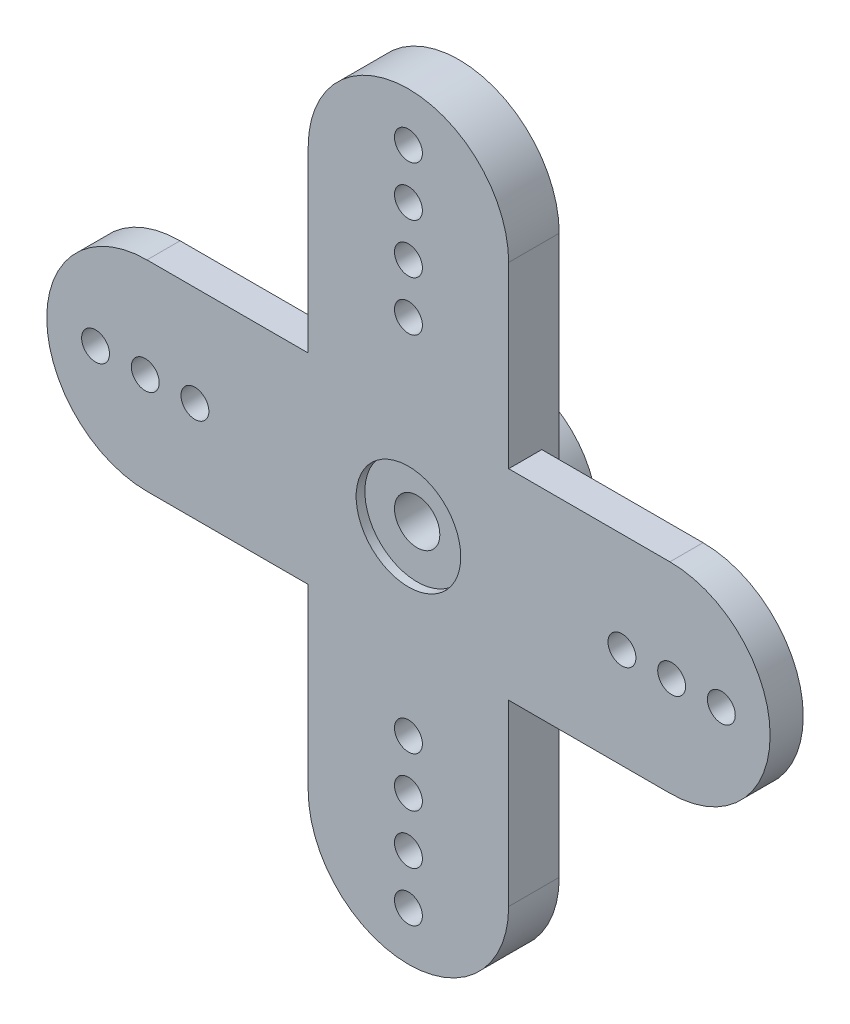
SolidWorks part; units mm, degrees
ref_plane "Front Plane" through (0, 0, 0) normal (0, 0, 1) x (1, 0, 0)
ref_plane "Top Plane" through (0, 0, 0) normal (0, 1, 0) x (1, 0, 0)
ref_plane "Right Plane" through (0, 0, 0) normal (1, 0, 0) x (0, 0, -1)
sketch "Sketch1" plane through (0, 0, 0) normal (0, 0, 1) x (1, 0, 0)
  line L0 (-5.75, 16) -> (-5.75, 5.75)
  line L1 (-15, 5.75) -> (-5.75, 5.75)
  line L2 (5.75, -16) -> (5.75, -5.75)
  line L3 (-15, -5.75) -> (-5.75, -5.75)
  line L4 (-5.75, -5.75) -> (-5.75, -16)
  line L5 (5.75, 5.75) -> (5.75, 16)
  line L6 (5.75, 5.75) -> (15, 5.75)
  line L7 (5.75, -5.75) -> (15, -5.75)
  arc A0 (5.75, 16) -> (-5.75, 16) centre (0, 16) ccw
  arc A1 (15, -5.75) -> (15, 5.75) centre (15, 0) ccw
  arc A2 (-15, 5.75) -> (-15, -5.75) centre (-15, 0) ccw
  arc A3 (-5.75, -16) -> (5.75, -16) centre (0, -16) ccw
  dimension "D1" = 11.5
  dimension "D2" = 11.5
  dimension "D3" = 11.5
  dimension "D4" = 11.5
  dimension "D5" = 32
  dimension "D6" = 30
  dimension "D7" = 16
  dimension "D8" = 15
extrude "Boss-Extrude1" add sketch "Sketch1" along normal blind 1.9
sketch "Sketch2" plane through (0, 0, 0) normal (0, 0, -1) x (-1, 0, 0)
  line L0 (-5.75, 16) -> (-5.75, -16)
  line L1 (5.75, 16) -> (5.75, 5.75) construction
  line L2 (5.75, -5.75) -> (5.75, -16) construction
  line L3 (5.75, 16) -> (5.75, 5.75)
  line L4 (5.75, -5.75) -> (5.75, -16)
  line L5 (5.75, 5.75) -> (5.75, -5.75)
  arc A0 (-5.75, -16) -> (5.75, -16) centre (0, -16) ccw construction
  arc A1 (5.75, 16) -> (-5.75, 16) centre (0, 16) ccw construction
  arc A2 (-5.75, -16) -> (5.75, -16) centre (0, -16) ccw
  arc A3 (5.75, 16) -> (-5.75, 16) centre (0, 16) ccw
extrude "Boss-Extrude2" add sketch "Sketch2" along normal blind 1
sketch "Sketch3" plane through (0, 0, 1.9) normal (0, 0, 1) x (1, 0, 0)
  circle A0 centre (0, 0) radius 3
extrude "Cut-Extrude1" cut sketch "Sketch3" against normal blind 0.5
sketch "Sketch4" plane through (0, 0, -1) normal (0, 0, -1) x (-1, 0, 0)
  circle A0 centre (0, 0) radius 4.825
  circle A1 centre (0, 0) radius 2.775
extrude "Boss-Extrude3" add sketch "Sketch4" along normal blind 3.1
sketch "Sketch5" plane through (0, 0, -1) normal (0, 0, -1) x (-1, 0, 0)
  circle A0 centre (0, 0) radius 1.3
extrude "Cut-Extrude2" cut sketch "Sketch5" against normal through all contours A0
sketch "Sketch6" plane through (0, 0, 1.9) normal (0, 0, 1) x (1, 0, 0)
  circle A0 centre (-17.95, 0) radius 0.8
  circle A1 centre (-15.1, 0) radius 0.8
  circle A2 centre (-12.25, 0) radius 0.8
  circle A3 centre (0, 18.95) radius 0.8
  circle A4 centre (0, 16.1) radius 0.8
  circle A5 centre (0, 13.25) radius 0.8
  circle A6 centre (12.25, 0) radius 0.8
  circle A7 centre (15.1, 0) radius 0.8
  circle A8 centre (17.95, 0) radius 0.8
  circle A9 centre (0, -10.4) radius 0.8
  circle A10 centre (0, -13.25) radius 0.8
  circle A11 centre (0, -16.1) radius 0.8
  circle A12 centre (0, -18.95) radius 0.8
  circle A13 centre (0, 10.4) radius 0.8
  arc A18 (15, -5.75) -> (15, 5.75) centre (15, 0) ccw construction
  arc A19 (5.75, 16) -> (-5.75, 16) centre (0, 16) ccw construction
  arc A20 (-15, 5.75) -> (-15, -5.75) centre (-15, 0) ccw construction
  arc A21 (-5.75, -16) -> (5.75, -16) centre (0, -16) ccw construction
  point P28 (0, 21.75)
  point P29 (0, -21.75)
  point P44 (20.75, 0)
  point P49 (0, 21.75)
  point P54 (-20.75, 0)
  point P58 (0, -21.75)
  dimension "D1" = 1.6
  dimension "D3" = 20.8
  dimension "D5" = 2.85
  dimension "D2" = 2.8
  dimension "D4" = 2.85
  dimension "D6" = 2.85
  dimension "D7" = 2.85
  dimension "D8" = 2.85
  dimension "D9" = 2.85
  dimension "D10" = 2.85
  dimension "D11" = 2.85
  dimension "D12" = 2.85
  dimension "D13" = 2.85
  dimension "D14" = 2.8
  dimension "D15" = 2.8
  dimension "D16" = 2.8
extrude "Cut-Extrude4" cut sketch "Sketch6" against normal through all
